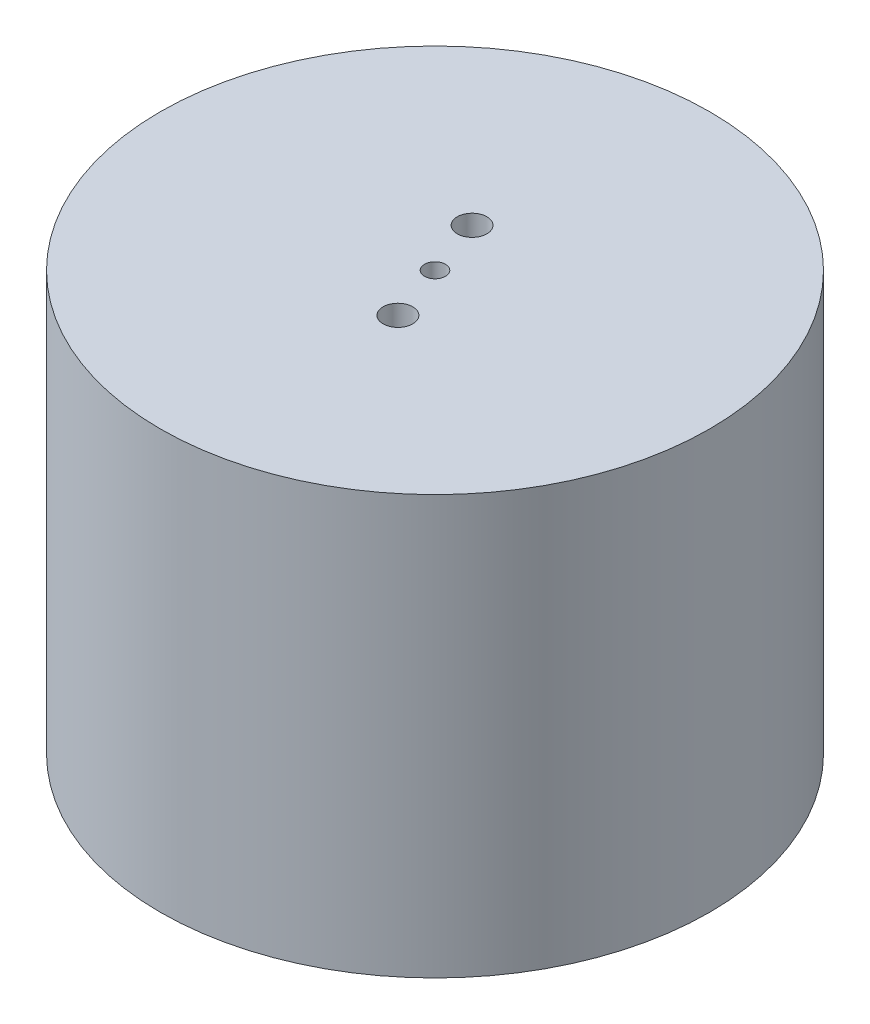
SolidWorks part; units mm, degrees
ref_plane "Front Plane" through (0, 0, 0) normal (0, 0, 1) x (1, 0, 0)
ref_plane "Top Plane" through (0, 0, 0) normal (0, 1, 0) x (1, 0, 0)
ref_plane "Right Plane" through (0, 0, 0) normal (1, 0, 0) x (0, 0, -1)
sketch "Sketch3" plane through (0, 0, 0) normal (0, 1, 0) x (1, 0, 0)
  circle A0 centre (0, 0) radius 26.5
  dimension "D1" = 53
sketch "Sketch4" plane through (0, 0, 0) normal (0, 1, 0) x (1, 0, 0)
  circle A0 centre (0, 0) radius 31.5
  circle A1 centre (0, 0) radius 26.5 construction
  dimension "D1" = 5
extrude "Boss-Extrude2" add sketch "Sketch4" along normal blind 48 contours A0
extrude "Cut-Extrude1" cut sketch "Sketch3" along normal blind 43 contours A0
sketch "Sketch5" plane through (0, 48, 0) normal (0, 1, 0) x (1, 0, 0)
  point P0 (0, 0)
sketch "Sketch7" plane through (0, 0, 0) normal (0, 0, 1) x (1, 0, 0)
  line L0 (0, 48) -> (0, 0)
hole_wizard "M3 Clearance Hole1" positions "Sketch9" profile "Sketch8" hole size "M3" standard "ANSI Metric"
sketch "Sketch9" plane through (0, 48, 0) normal (0, 1, 0) x (1, 0, 0)
  point P0 (-2.345, 6.5955)
  point P2 (2.345, -6.5955)
  dimension "D1" = 7
  dimension "D2" = 7
  dimension "D3" = 180
sketch "Sketch8" plane through (-2.345, 48, -6.5955) normal (1, 0, 0) x (0, 0, 1)
  line L0 (0, 0) -> (0, 51.0215)
  line L1 (0, 51.0215) -> (1.7, 50)
  line L2 (1.7, 50) -> (1.7, 0)
  line L5 (1.7, 0) -> (0, 0)
  line L10 (0, 51.0215) -> (-1.7, 50) construction
  line L11 (0, -6.35) -> (0, 107.95) construction
  dimension "Hole Dia." = 3.4
  dimension "Hole Depth" = 50
  dimension "Drill Angle" = 118
sketch "Sketch10" plane through (0, 48, 0) normal (0, 1, 0) x (1, 0, 0)
  circle A0 centre (0, 0) radius 1.2
extrude "Cut-Extrude2" cut sketch "Sketch10" against normal blind 10
sketch "Sketch11" plane through (0, 48, 0) normal (0, 1, 0) x (1, 0, 0)
  line L0 (-2.345, 6.5955) -> (2.345, -6.5955)
sketch "Sketch12" plane through (0, 48, 0) normal (0, 1, 0) x (1, 0, 0)
  line L0 (5.3523, 14.7968) -> (15.4025, -13.4697)
  line L1 (-2.345, 6.5955) -> (2.345, -6.5955) construction
  dimension "D1" = 10
sketch "Sketch13" plane through (0, 48, 0) normal (0, 1, 0) x (1, 0, 0)
  line L0 (-8.1183, -20.9291) -> (17.19, -11.9306)
  line L1 (-2.345, 6.5955) -> (2.345, -6.5955) construction
  dimension "D1" = 10
